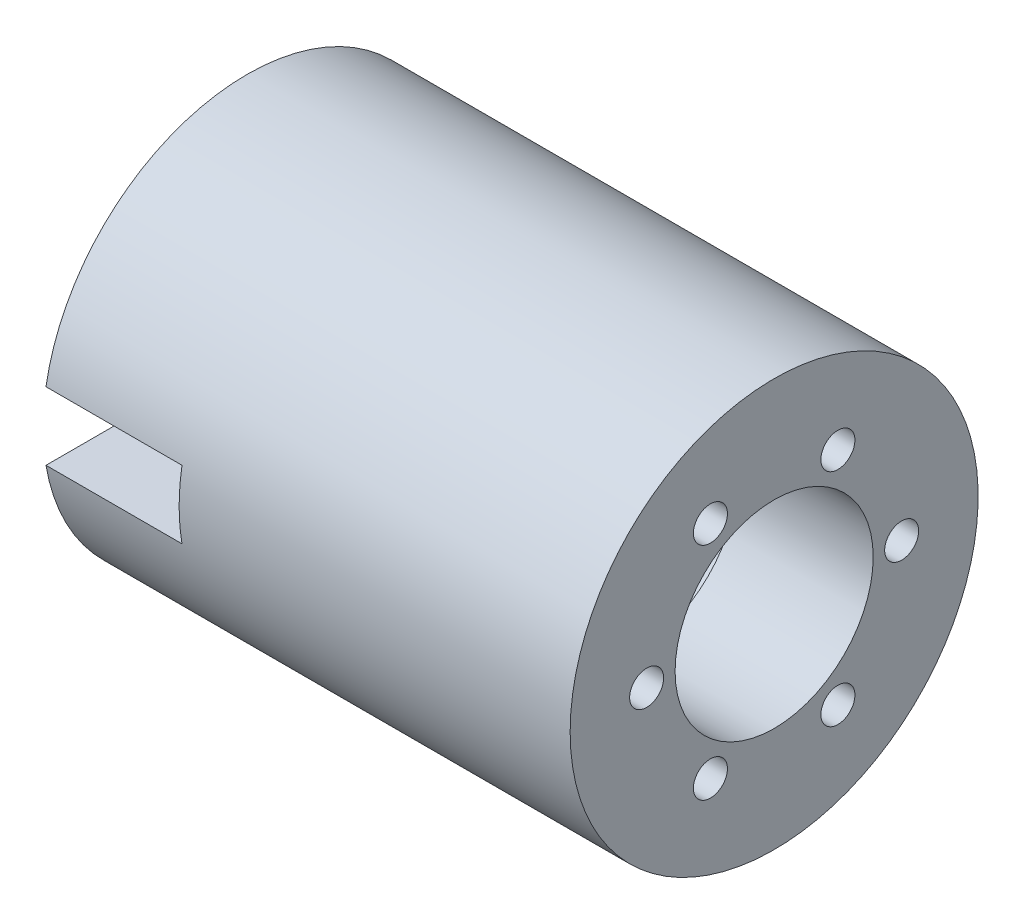
SolidWorks part; units mm, degrees
ref_plane "Front Plane" through (0, 0, 0) normal (0, 0, 1) x (1, 0, 0)
ref_plane "Top Plane" through (0, 0, 0) normal (0, 1, 0) x (1, 0, 0)
ref_plane "Right Plane" through (0, 0, 0) normal (1, 0, 0) x (0, 0, -1)
sketch "Sketch1" plane through (0, 0, 0) normal (0, 0, 1) x (1, 0, 0)
  line L0 (-49.2125, 0) -> (49.2125, 0) construction
  line L1 (0, 0) -> (0, 21.2725) construction
  line L2 (-49.2125, 21.2725) -> (49.2125, 21.2725)
  line L3 (-49.2125, 21.2725) -> (-49.2125, 38.1)
  line L4 (-49.2125, 38.1) -> (42.8625, 38.1)
  line L5 (42.8625, 38.1) -> (42.8625, 76.2)
  line L6 (42.8625, 76.2) -> (49.2125, 76.2)
  line L7 (49.2125, 76.2) -> (49.2125, 21.2725)
  line L8 (42.8625, 38.1) -> (49.2125, 38.1)
  line L9 (23.8125, 21.2725) -> (23.8125, 15.875)
  line L10 (23.8125, 15.875) -> (49.2125, 15.875)
  line L11 (49.2125, 15.875) -> (49.2125, 21.2725)
  point P4 (0, 0)
  point P10 (0, 21.2725)
  dimension "D1" = 6.35
  dimension "D2" = 21.2725
  dimension "D3" = 98.425
  dimension "D4" = 76.2
  dimension "D5" = 38.1
  dimension "D6" = 25.4
  dimension "D7" = 15.875
revolve "Revolve1" add sketch "Sketch1" angle 360 about L0
sketch "Sketch2" plane through (49.2125, 0, 0) normal (1, 0, 0) x (0, 0, -1)
  line L0 (-9.316, 41.6349) -> (-4.7427, 53.3559)
  line L1 (31.3989, 28.8853) -> (43.8362, 30.7853)
  line L2 (40.7149, -12.7495) -> (48.5789, -22.5706)
  line L3 (9.316, -41.6349) -> (4.7427, -53.3559)
  line L4 (-31.3989, -28.8853) -> (-43.8362, -30.7853)
  line L5 (-40.7149, 12.7495) -> (-48.5789, 22.5706)
  circle A0 centre (0, 0) radius 80
  circle A1 centre (0, 68) radius 2.5
  circle A2 centre (8.3322, 73.5294) radius 2.5
  circle A3 centre (17.5997, 65.683) radius 2.5
  circle A4 centre (27.0791, 68.8674) radius 2.5
  circle A5 centre (34, 58.8897) radius 2.5
  circle A6 centre (43.9806, 59.5122) radius 2.5
  circle A7 centre (48.0833, 48.0833) radius 2.5
  circle A8 centre (57.8849, 46.1014) radius 2.5
  circle A9 centre (58.8897, 34) radius 2.5
  circle A10 centre (67.8444, 29.5488) radius 2.5
  circle A11 centre (65.683, 17.5997) radius 2.5
  circle A12 centre (73.1805, 10.9825) radius 2.5
  circle A13 centre (68, 0) radius 2.5
  circle A14 centre (73.5294, -8.3322) radius 2.5
  circle A15 centre (65.683, -17.5997) radius 2.5
  circle A16 centre (68.8674, -27.0791) radius 2.5
  circle A17 centre (58.8897, -34) radius 2.5
  circle A18 centre (59.5122, -43.9806) radius 2.5
  circle A19 centre (48.0833, -48.0833) radius 2.5
  circle A20 centre (46.1014, -57.8849) radius 2.5
  circle A21 centre (34, -58.8897) radius 2.5
  circle A22 centre (29.5488, -67.8444) radius 2.5
  circle A23 centre (17.5997, -65.683) radius 2.5
  circle A24 centre (10.9825, -73.1805) radius 2.5
  circle A25 centre (0, -68) radius 2.5
  circle A26 centre (-8.3322, -73.5294) radius 2.5
  circle A27 centre (-17.5997, -65.683) radius 2.5
  circle A28 centre (-27.0791, -68.8674) radius 2.5
  circle A29 centre (-34, -58.8897) radius 2.5
  circle A30 centre (-43.9806, -59.5122) radius 2.5
  circle A31 centre (-48.0833, -48.0833) radius 2.5
  circle A32 centre (-57.8849, -46.1014) radius 2.5
  circle A33 centre (-58.8897, -34) radius 2.5
  circle A34 centre (-67.8444, -29.5488) radius 2.5
  circle A35 centre (-65.683, -17.5997) radius 2.5
  circle A36 centre (-73.1805, -10.9825) radius 2.5
  circle A37 centre (-68, 0) radius 2.5
  circle A38 centre (-73.5294, 8.3322) radius 2.5
  circle A39 centre (-65.683, 17.5997) radius 2.5
  circle A40 centre (-68.8674, 27.0791) radius 2.5
  circle A41 centre (-58.8897, 34) radius 2.5
  circle A42 centre (-59.5122, 43.9806) radius 2.5
  circle A43 centre (-48.0833, 48.0833) radius 2.5
  circle A44 centre (-46.1014, 57.8849) radius 2.5
  circle A45 centre (-34, 58.8897) radius 2.5
  circle A46 centre (-29.5488, 67.8444) radius 2.5
  circle A47 centre (-17.5997, 65.683) radius 2.5
  circle A48 centre (-10.9825, 73.1805) radius 2.5
  circle A49 centre (0, 0) radius 18.5
  circle A50 centre (-11.9063, 20.6222) radius 3.175
  circle A51 centre (11.9063, 20.6222) radius 3.175
  circle A52 centre (23.8125, 0) radius 3.175
  circle A53 centre (11.9063, -20.6222) radius 3.175
  circle A54 centre (-11.9063, -20.6222) radius 3.175
  spline S0 degree 2 poles (5.9532, 60.7088) (27.9941, 58.3228) (43.6425, 42.6185) knots 0 0 0 1 1 1
  spline S1 degree 2 poles (4.0813, 28.8708) (21.9975, 36.8421) (41.5951, 37.5241) knots 0 0 0 1 1 1
  spline S2 degree 1 poles (-10, 38) (-9.316, 41.6349) knots 0 0 1 1
  spline S3 degree 3 poles (-4.7427, 53.3559) (-3.6172, 58.1411) (1.3644, 61.1789) (5.9532, 60.7088) knots 0 0 0 0 1 1 1 1
  spline S4 degree 3 poles (4.0813, 28.8708) (-1.8873, 26.0232) (-10.3042, 30.435) (-10, 38) knots 0 0 0 0 1 1 1 1
  spline S5 degree 2 poles (41.5951, 37.5241) (45.9407, 38.7363) (43.6425, 42.6185) knots 0 0 0 1 1 1
  spline S6 degree 2 poles (53.2944, -17.2603) (56.5169, -20.4176) (58.7299, -16.4862) knots 0 0 0 1 1 1
  spline S7 degree 2 poles (55.552, 25.1988) (64.506, 4.9178) (58.7299, -16.4862) knots 0 0 0 1 1 1
  spline S8 degree 3 poles (43.8362, 30.7853) (48.5431, 32.2031) (53.6647, 29.4078) (55.552, 25.1988) knots 0 0 0 0 1 1 1 1
  spline S9 degree 1 poles (27.909, 27.6603) (31.3989, 28.8853) knots 0 0 1 1
  spline S10 degree 3 poles (27.0435, 10.9008) (21.5931, 14.646) (21.2054, 24.1412) (27.909, 27.6603) knots 0 0 0 0 1 1 1 1
  spline S11 degree 2 poles (27.0435, 10.9008) (42.905, -0.6293) (53.2944, -17.2603) knots 0 0 0 1 1 1
  spline S12 degree 2 poles (11.6993, -54.7845) (10.5763, -59.1539) (15.0875, -59.1047) knots 0 0 0 1 1 1
  spline S13 degree 2 poles (49.5988, -35.51) (36.5119, -53.405) (15.0875, -59.1047) knots 0 0 0 1 1 1
  spline S14 degree 3 poles (48.5789, -22.5706) (52.1602, -25.938) (52.3003, -31.7711) (49.5988, -35.51) knots 0 0 0 0 1 1 1 1
  spline S15 degree 1 poles (37.909, -10.3397) (40.7149, -12.7495) knots 0 0 1 1
  spline S16 degree 3 poles (22.9622, -17.9699) (23.4804, -11.3771) (31.5096, -6.2938) (37.909, -10.3397) knots 0 0 0 0 1 1 1 1
  spline S17 degree 2 poles (22.9622, -17.9699) (20.9075, -37.4715) (11.6993, -54.7845) knots 0 0 0 1 1 1
  spline S18 degree 2 poles (-41.5951, -37.5241) (-45.9407, -38.7363) (-43.6425, -42.6185) knots 0 0 0 1 1 1
  spline S19 degree 2 poles (-5.9532, -60.7088) (-27.9941, -58.3228) (-43.6425, -42.6185) knots 0 0 0 1 1 1
  spline S20 degree 3 poles (4.7427, -53.3559) (3.6172, -58.1411) (-1.3644, -61.1789) (-5.9532, -60.7088) knots 0 0 0 0 1 1 1 1
  spline S21 degree 1 poles (10, -38) (9.316, -41.6349) knots 0 0 1 1
  spline S22 degree 3 poles (-4.0813, -28.8708) (1.8873, -26.0232) (10.3042, -30.435) (10, -38) knots 0 0 0 0 1 1 1 1
  spline S23 degree 2 poles (-4.0813, -28.8708) (-21.9975, -36.8421) (-41.5951, -37.5241) knots 0 0 0 1 1 1
  spline S24 degree 2 poles (-53.2944, 17.2603) (-56.5169, 20.4176) (-58.7299, 16.4862) knots 0 0 0 1 1 1
  spline S25 degree 2 poles (-55.552, -25.1988) (-64.506, -4.9178) (-58.7299, 16.4862) knots 0 0 0 1 1 1
  spline S26 degree 3 poles (-43.8362, -30.7853) (-48.5431, -32.2031) (-53.6647, -29.4078) (-55.552, -25.1988) knots 0 0 0 0 1 1 1 1
  spline S27 degree 1 poles (-27.909, -27.6603) (-31.3989, -28.8853) knots 0 0 1 1
  spline S28 degree 3 poles (-27.0435, -10.9008) (-21.5931, -14.646) (-21.2054, -24.1412) (-27.909, -27.6603) knots 0 0 0 0 1 1 1 1
  spline S29 degree 2 poles (-27.0435, -10.9008) (-42.905, 0.6293) (-53.2944, 17.2603) knots 0 0 0 1 1 1
  spline S30 degree 2 poles (-11.6993, 54.7845) (-10.5763, 59.1539) (-15.0875, 59.1047) knots 0 0 0 1 1 1
  spline S31 degree 2 poles (-49.5988, 35.51) (-36.5119, 53.405) (-15.0875, 59.1047) knots 0 0 0 1 1 1
  spline S32 degree 3 poles (-48.5789, 22.5706) (-52.1602, 25.938) (-52.3003, 31.7711) (-49.5988, 35.51) knots 0 0 0 0 1 1 1 1
  spline S33 degree 1 poles (-37.909, 10.3397) (-40.7149, 12.7495) knots 0 0 1 1
  spline S34 degree 3 poles (-22.9622, 17.9699) (-23.4804, 11.3771) (-31.5096, 6.2938) (-37.909, 10.3397) knots 0 0 0 0 1 1 1 1
  spline S35 degree 2 poles (-22.9622, 17.9699) (-20.9075, 37.4715) (-11.6993, 54.7845) knots 0 0 0 1 1 1
extrude "Cut-Extrude1" cut sketch "Sketch2" against normal blind 25.4 contours A54 | A53 | A52 | A51 | A50 | A49
pattern_circular "CirPattern1" count 6 over 360 about axis through (-49.2125, 0, 0) along (-1, 0, 0) of "Cut-Extrude1"
sketch "Sketch3" plane through (0, 0, 0) normal (0, 0, 1) x (1, 0, 0)
  line L0 (0, 0) -> (-49.2125, 0) construction
  line L1 (-49.2125, 38.1) -> (-49.2125, -38.1) construction
  line L2 (-49.2125, -6.35) -> (-49.2125, 6.35)
  line L3 (-49.2125, 6.35) -> (-23.8125, 6.35)
  line L4 (-23.8125, 6.35) -> (-23.8125, -6.35)
  line L5 (-23.8125, -6.35) -> (-49.2125, -6.35)
  point P8 (-49.2125, 0)
  dimension "D1" = 12.7
  dimension "D2" = 25.4
extrude "Cut-Extrude2" cut sketch "Sketch3" along normal through all
